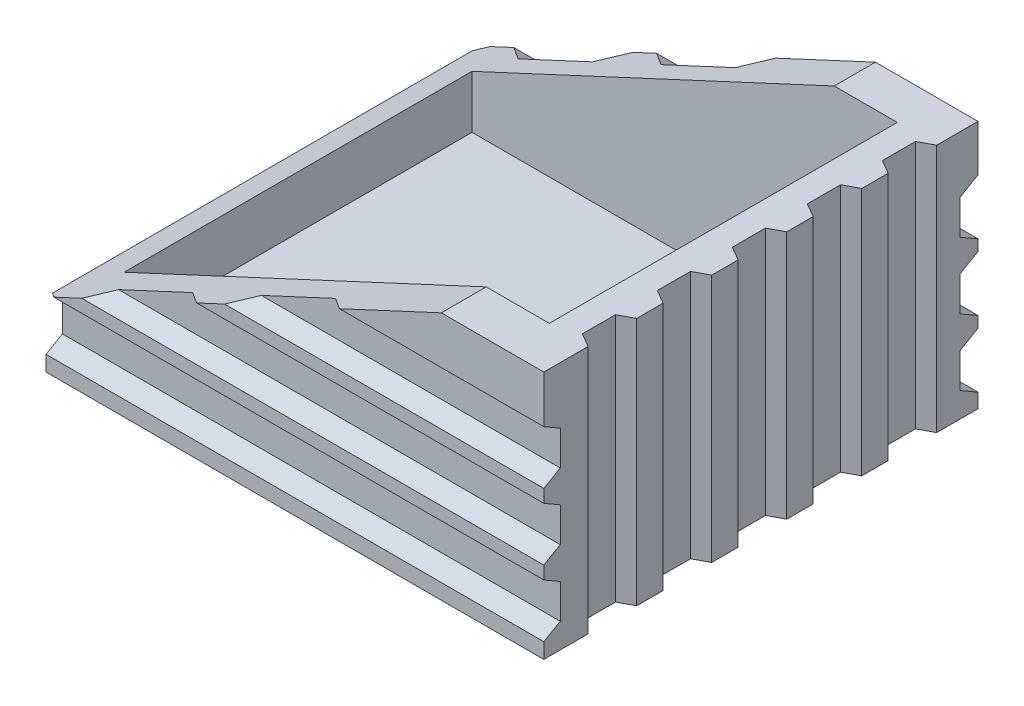
SolidWorks part; units mm, degrees
ref_plane "Front Plane" through (0, 0, 0) normal (0, 0, 1) x (1, 0, 0)
ref_plane "Top Plane" through (0, 0, 0) normal (0, 1, 0) x (1, 0, 0)
ref_plane "Right Plane" through (0, 0, 0) normal (1, 0, 0) x (0, 0, -1)
sketch "Sketch3" plane through (0, 0, 0) normal (0, 1, 0) x (1, 0, 0)
  line L1 (-0.045, -0.0405) -> (0.045, -0.0405)
  line L2 (-0.045, -0.0405) -> (-0.045, 0.0405)
  line L3 (-0.045, 0.0405) -> (0.045, 0.0405)
  line L4 (0.045, -0.0405) -> (0.045, 0.0405)
  line L5 (-0.045, -0.0405) -> (0.045, 0.0405) construction
  line L6 (-0.045, 0.0405) -> (0.045, -0.0405) construction
  point P0 (0, 0)
  dimension "D1" = 0.09
  dimension "D2" = 0.0811
extrude "Boss-Extrude2" add sketch "Sketch3" along normal blind 0.045
sketch "Sketch4" plane through (0, 0.045, 0) normal (0, 1, 0) x (1, 0, 0)
  line L1 (-0.039, 0.0331) -> (0.0379, 0.0331)
  line L2 (-0.039, 0.0331) -> (-0.039, -0.0298)
  line L3 (-0.039, -0.0298) -> (0.0379, -0.0298)
  line L4 (0.0379, 0.0331) -> (0.0379, -0.0298)
extrude "Cut-Extrude2" cut sketch "Sketch4" against normal blind 0.04
sketch "Sketch5" plane through (0, 0, -0.0405) normal (0, 0, -1) x (-1, 0, 0)
  line L0 (-0.0265, 0.045) -> (0.045, 0.045)
  line L1 (-0.045, 0.045) -> (0.045, 0.045) construction
  line L2 (0.045, 0.045) -> (0.045, 0.0118)
  line L3 (0.045, 0.045) -> (0.045, 0) construction
  line L4 (0.045, 0.0118) -> (-0.0265, 0.045)
extrude "Cut-Extrude3" cut sketch "Sketch5" against normal blind 0.085
sketch "Sketch6" plane through (0, 0.045, 0) normal (0, 1, 0) x (1, 0, 0)
  line L0 (0.0379, 0.0331) -> (0.045, 0.0331) construction
  line L1 (0.045, -0.0405) -> (0.045, 0.0405) construction
  line L2 (0.045, 0.0331) -> (0.0425, 0.0317)
  line L3 (0.0425, 0.0317) -> (0.0425, 0.0257)
  line L4 (0.0425, 0.0257) -> (0.045, 0.0243)
  line L5 (0.045, 0.0243) -> (0.045, 0.0331)
  line L6 (0.045, 0.0195) -> (0.0425, 0.0182)
  line L7 (0.0425, 0.0182) -> (0.0425, 0.0122)
  line L8 (0.045, 0.0107) -> (0.045, 0.0195)
  line L9 (0.0425, 0.0122) -> (0.045, 0.0107)
  line L10 (0.045, 0.006) -> (0.0425, 0.0046)
  line L11 (0.0425, 0.0046) -> (0.0425, -0.0014)
  line L12 (0.045, -0.0028) -> (0.045, 0.006)
  line L13 (0.0425, -0.0014) -> (0.045, -0.0028)
  line L14 (0.045, -0.0076) -> (0.0425, -0.0089)
  line L15 (0.0425, -0.0089) -> (0.0425, -0.0149)
  line L16 (0.045, -0.0164) -> (0.045, -0.0076)
  line L17 (0.0425, -0.0149) -> (0.045, -0.0164)
  line L18 (0.045, -0.0212) -> (0.0425, -0.0225)
  line L19 (0.0425, -0.0225) -> (0.0425, -0.0285)
  line L20 (0.045, -0.0299) -> (0.045, -0.0212)
  line L21 (0.0425, -0.0285) -> (0.045, -0.0299)
  dimension "D1" = 118.113
  dimension "D2" = 120
  dimension "D3" = 0.0025
  dimension "D4" = 0.006
  dimension "D5" = 5
extrude "Cut-Extrude5" cut sketch "Sketch6" against normal blind 0.045
sketch "Sketch8" plane through (0.045, 0, 0) normal (1, 0, 0) x (0, 0, -1)
  line L0 (0.0405, 0.0366) -> (0.0405, 0.0266)
  line L1 (0.0405, 0.045) -> (0.0405, 0) construction
  line L2 (0.0405, 0.0266) -> (0.0373, 0.0285)
  line L5 (0.0405, 0.0366) -> (0.0373, 0.0347)
  line L6 (0.0373, 0.0347) -> (0.0373, 0.0285)
  line L7 (0.0331, 0.045) -> (0.0405, 0.045) construction
  line L8 (0.0373, 0.0227) -> (0.0373, 0.0165)
  line L9 (0.0405, 0.0146) -> (0.0373, 0.0165)
  line L10 (0.0405, 0.0246) -> (0.0405, 0.0146)
  line L11 (0.0405, 0.0246) -> (0.0373, 0.0227)
  line L12 (0.0373, 0.0107) -> (0.0373, 0.0045)
  line L13 (0.0405, 0.0026) -> (0.0373, 0.0045)
  line L14 (0.0405, 0.0126) -> (0.0405, 0.0026)
  line L15 (0.0405, 0.0126) -> (0.0373, 0.0107)
  line L23 (0.0012, 0.0466) -> (0.0012, 0.0014) construction
  line L24 (-0.0382, 0.0126) -> (-0.035, 0.0107)
  line L25 (-0.0382, 0.0126) -> (-0.0382, 0.0026)
  line L26 (-0.0382, 0.0026) -> (-0.035, 0.0045)
  line L27 (-0.035, 0.0107) -> (-0.035, 0.0045)
  line L28 (-0.0382, 0.0246) -> (-0.035, 0.0227)
  line L29 (-0.0382, 0.0246) -> (-0.0382, 0.0146)
  line L30 (-0.0382, 0.0146) -> (-0.035, 0.0165)
  line L31 (-0.035, 0.0227) -> (-0.035, 0.0165)
  line L32 (-0.0382, 0.0366) -> (-0.035, 0.0347)
  line L33 (-0.0382, 0.0366) -> (-0.0382, 0.0266)
  line L34 (-0.0382, 0.0266) -> (-0.035, 0.0285)
  line L35 (-0.035, 0.0347) -> (-0.035, 0.0285)
  dimension "D1" = 120
  dimension "D2" = 120
  dimension "D3" = 0.0033
  dimension "D4" = 0.0062
  dimension "D5" = 0.0184
  dimension "D6" = 3
extrude "Cut-Extrude6" cut sketch "Sketch8" against normal blind 0.095
sketch "Sketch10" plane through (0.045, 0, 0) normal (1, 0, 0) x (0, 0, -1)
  line L0 (-0.0405, 0) -> (-0.0299, 0) construction
  line L1 (-0.0405, 0.045) -> (-0.0379, 0.045)
  line L2 (-0.0405, 0.045) -> (-0.0405, 0)
  line L3 (-0.0405, 0) -> (-0.0379, 0)
  line L4 (-0.0379, 0.045) -> (-0.0379, 0)
  dimension "D1" = 0.0026
extrude "Cut-Extrude7" cut sketch "Sketch10" against normal blind 0.095
